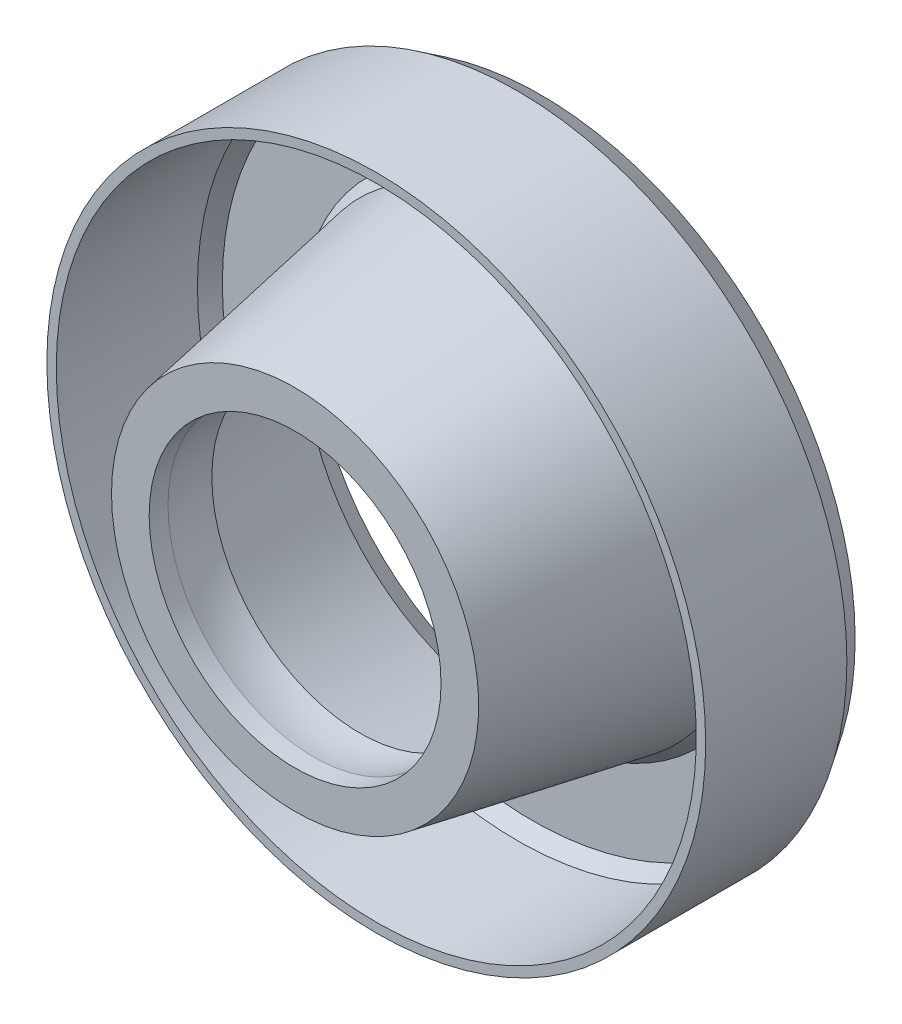
SolidWorks part; units mm, degrees
ref_plane "Front Plane" through (0, 0, 0) normal (0, 0, 1) x (1, 0, 0)
ref_plane "Top Plane" through (0, 0, 0) normal (0, 1, 0) x (1, 0, 0)
ref_plane "Right Plane" through (0, 0, 0) normal (1, 0, 0) x (0, 0, -1)
sketch "Sketch4" plane through (0, 0, 0) normal (0, 1, 0) x (1, 0, 0)
  line L0 (-10.9333, -10.9667) -> (-9.9333, -10.9667)
  line L1 (-9.9333, -10.9667) -> (-9.9333, 4.0333)
  line L2 (-10.9333, -10.9667) -> (-10.9333, 4.0333)
  line L3 (-10.9333, 4.0333) -> (-9.2969, 6.5477)
  line L4 (-9.9333, 4.0333) -> (-8.8909, 5.6349)
  line L5 (-8.8909, 5.6349) -> (-0.7028, 5.6349)
  line L6 (-4.7969, 6.5477) -> (-4.7969, -11.4756) construction
  line L7 (-9.2969, 6.5477) -> (-0.2969, 6.5477)
  line L8 (1.3396, 4.0333) -> (-0.2969, 6.5477)
  line L9 (0.3396, 4.0333) -> (-0.7028, 5.6349)
  line L10 (24.0667, 10.346) -> (24.0667, -27.6077) construction
  line L11 (0.3396, 4.0333) -> (4.5622, -19.5923)
  line L12 (1.3396, 4.0333) -> (4.3306, -12.7015)
  line L13 (4.3306, -12.7015) -> (8.3306, -12.7015)
  line L14 (4.5622, -19.5923) -> (8.5622, -19.5923)
  line L15 (8.5622, -19.5923) -> (8.5622, -17.5923)
  arc A0 (8.3306, -12.7015) -> (8.5622, -17.5923) centre (24.0667, -14.4073) ccw
  dimension "D1" = 1
  dimension "D2" = 15
  dimension "D3" = 15
  dimension "D4" = 3
  dimension "D5" = 9
  dimension "D6" = 35
  dimension "D7" = 24
  dimension "D8" = 17
  dimension "D9" = 4
  dimension "D10" = 4
  dimension "D11" = 2
revolve "Revolve1" add sketch "Sketch4" angle 360 about L10
